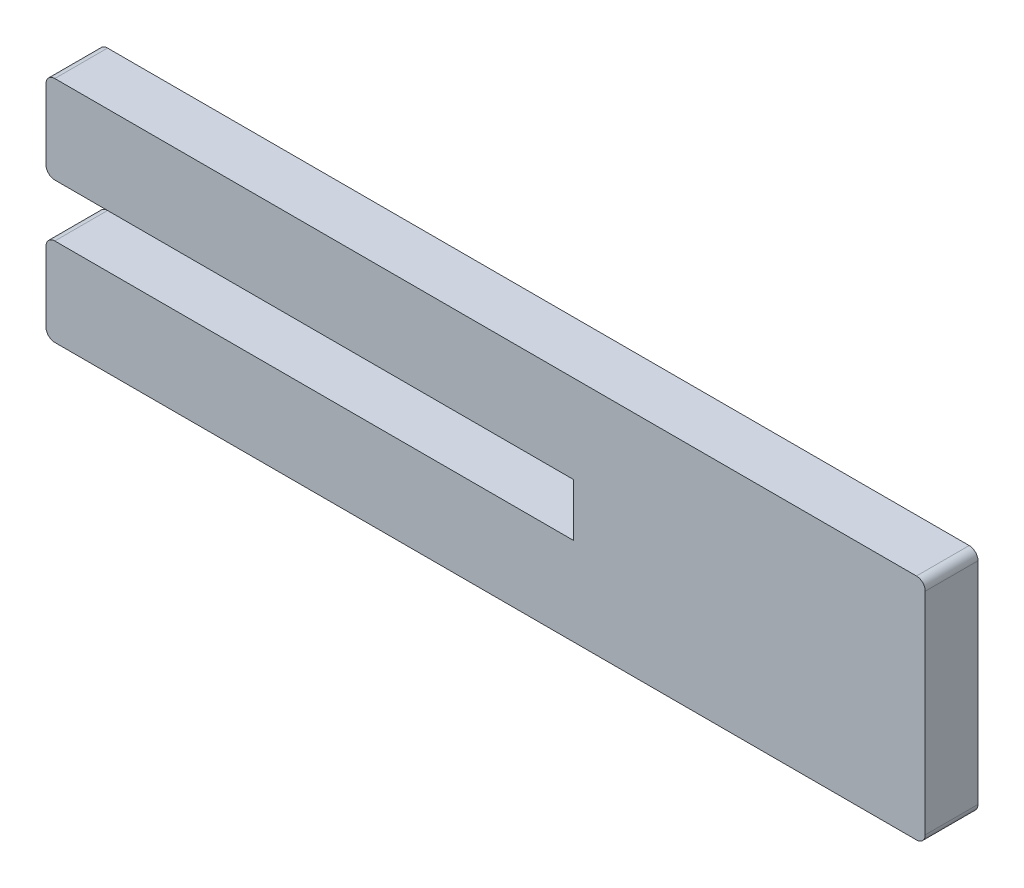
SolidWorks part; units mm, degrees
ref_plane "Alzado" through (0, 0, 0) normal (0, 0, 1) x (1, 0, 0)
ref_plane "Planta" through (0, 0, 0) normal (0, 1, 0) x (1, 0, 0)
ref_plane "Vista lateral" through (0, 0, 0) normal (1, 0, 0) x (0, 0, -1)
sketch "Croquis1" plane through (0, 0, 0) normal (0, 0, 1) x (1, 0, 0)
  line L0 (-29.5, 1.5) -> (0, 1.5)
  line L1 (0, 1.5) -> (0, -1.5)
  line L2 (0, 0) -> (-2.9667, 0) construction
  line L3 (-30, 2) -> (-30, 6)
  line L4 (-29.5, 6.5) -> (19.5, 6.5)
  line L5 (20, 6) -> (20, 0)
  line L6 (20, -6) -> (20, 0)
  line L7 (-29.5, -6.5) -> (19.5, -6.5)
  line L8 (-30, -2) -> (-30, -6)
  line L9 (-29.5, -1.5) -> (0, -1.5)
  arc A0 (-30, -2) -> (-29.5, -1.5) centre (-29.5, -2) cw
  arc A1 (-29.5, -6.5) -> (-30, -6) centre (-29.5, -6) cw
  arc A2 (20, -6) -> (19.5, -6.5) centre (19.5, -6) cw
  arc A3 (19.5, 6.5) -> (20, 6) centre (19.5, 6) cw
  arc A4 (-30, 6) -> (-29.5, 6.5) centre (-29.5, 6) cw
  arc A5 (-29.5, 1.5) -> (-30, 2) centre (-29.5, 2) cw
  point P16 (-30, -1.5)
  point P19 (-30, -6.5)
  point P22 (20, -6.5)
  point P25 (20, 6.5)
  point P28 (-30, 6.5)
  point P31 (-30, 1.5)
  dimension "D5" = 0.5
  dimension "D1" = 1.5
  dimension "D2" = 5
  dimension "D3" = 50
  dimension "D4" = 20
extrude "Saliente-Extruir1" add sketch "Croquis1" along normal blind 3
